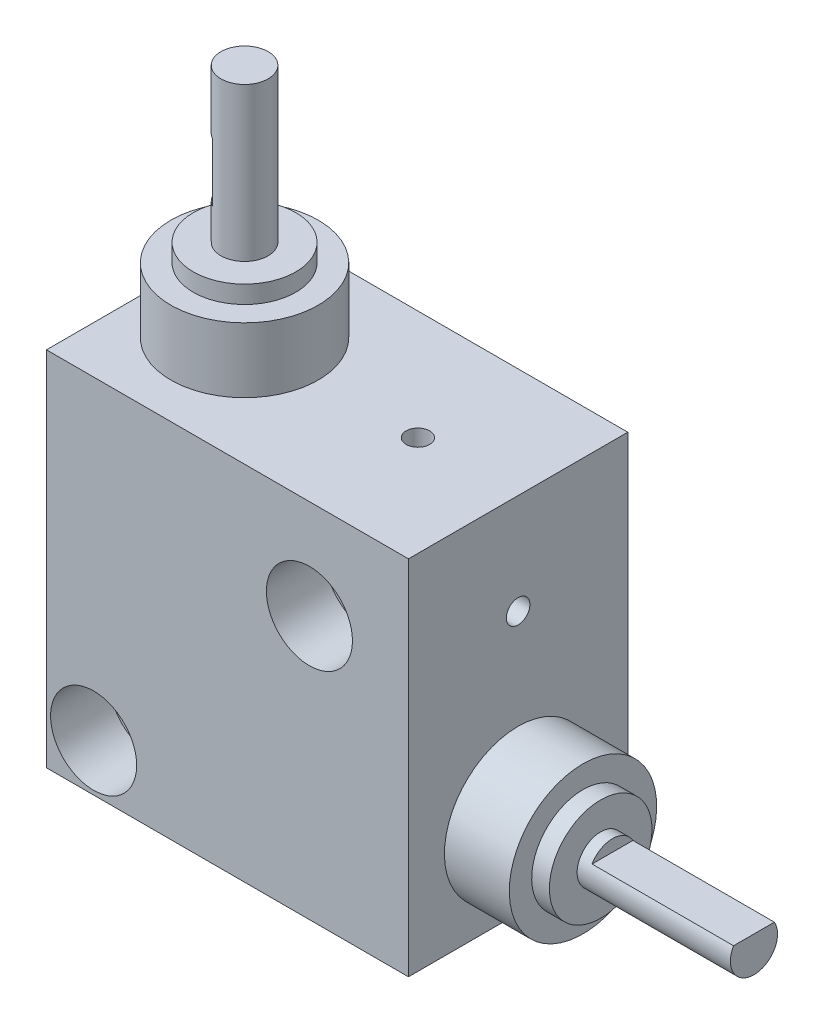
SolidWorks part; units mm, degrees
ref_plane "Plan de face" through (0, 0, 0) normal (0, 0, 1) x (1, 0, 0)
ref_plane "Plan de dessus" through (0, 0, 0) normal (0, 1, 0) x (1, 0, 0)
ref_plane "Plan de droite" through (0, 0, 0) normal (1, 0, 0) x (0, 0, -1)
sketch "Esquisse1" plane through (0, 0, 0) normal (0, 0, 1) x (1, 0, 0)
  line L1 (0, 0) -> (30.7, 0)
  line L2 (0, 0) -> (0, 30.7)
  line L3 (0, 30.7) -> (30.7, 30.7)
  line L4 (30.7, 0) -> (30.7, 30.7)
  dimension "D1" = 30.7
  dimension "D2" = 30.7
extrude "Boss.-Extru.1" add sketch "Esquisse1" along normal mid plane 18.6
sketch "Esquisse2" plane through (0, 0, 9.3) normal (0, 0, 1) x (1, 0, 0)
  line L0 (0, 0) -> (30.7, 0) construction
  line L2 (30.7, 0) -> (30.7, 30.7) construction
  line L3 (30.7, 30.7) -> (0, 30.7) construction
  line L5 (0, 30.7) -> (0, 0) construction
  circle A0 centre (4, 4) radius 2
  circle A1 centre (22.3, 22.3) radius 2
  dimension "D1" = 4
  dimension "D4" = 4
  dimension "D2" = 4
  dimension "D3" = 26.7
  dimension "D5" = 8.4
  dimension "D6" = 8.4
  dimension "D7" = 26.7
  dimension "D8" = 22.3
  dimension "D9" = 22.3
extrude "Enlèv. mat.-Extru.1" cut sketch "Esquisse2" against normal through all
sketch "Esquisse3" plane through (0, 0, 9.3) normal (0, 0, 1) x (1, 0, 0)
  circle A0 centre (4, 4) radius 3.65
  circle A1 centre (4, 4) radius 2 construction
  circle A2 centre (22.3, 22.3) radius 3.65
  circle A3 centre (22.3, 22.3) radius 2 construction
  dimension "D1" = 7.3
extrude "Enlèv. mat.-Extru.2" cut sketch "Esquisse3" against normal blind 5
sketch "Esquisse4" plane through (0, 0, -9.3) normal (0, 0, -1) x (-1, 0, 0)
  circle A0 centre (-4, 4) radius 3.65
  circle A1 centre (-22.3, 22.3) radius 3.65
  circle A2 centre (-22.3, 22.3) radius 2 construction
  dimension "D1" = 7.3
  dimension "D2" = 7.3
extrude "Enlèv. mat.-Extru.3" cut sketch "Esquisse4" against normal blind 5
sketch "Esquisse6" plane through (0, 0, 0) normal (0, 0, 1) x (1, 0, 0)
  line L0 (30.7, 13.75) -> (36.2, 13.75)
  line L1 (36.2, 13.75) -> (36.2, 11.85)
  line L2 (36.2, 11.85) -> (37.7, 11.85)
  line L3 (37.7, 11.85) -> (37.7, 9.5)
  line L4 (37.7, 9.5) -> (50.7, 9.5)
  line L5 (50.7, 9.5) -> (50.7, 7.5)
  line L6 (50.7, 7.5) -> (30.7, 7.5)
  line L7 (30.7, 0) -> (30.7, 30.7) construction
  line L8 (30.7, 7.5) -> (30.7, 13.75)
  line L9 (0, 0) -> (30.7, 0) construction
  dimension "D1" = 2
  dimension "D2" = 20
  dimension "D3" = 5.5
  dimension "D4" = 1.5
  dimension "D5" = 6.25
  dimension "D6" = 7.5
  dimension "D7" = 4.35
revolve "Révolution1" add sketch "Esquisse6" angle 360 about L6
sketch "Esquisse8" plane through (0, 0, 0) normal (0, 0, 1) x (1, 0, 0)
  line L0 (1.25, 30.7) -> (1.25, 36.2)
  line L1 (1.25, 36.2) -> (3.15, 36.2)
  line L2 (3.15, 36.2) -> (3.15, 37.7)
  line L3 (3.15, 37.7) -> (5.5, 37.7)
  line L4 (5.5, 37.7) -> (5.5, 50.7)
  line L5 (5.5, 50.7) -> (7.5, 50.7)
  line L6 (7.5, 50.7) -> (7.5, 30.7)
  line L7 (7.5, 30.7) -> (1.25, 30.7)
  line L8 (30.7, 30.7) -> (0, 30.7) construction
  line L9 (0, 30.7) -> (0, 0) construction
  dimension "D1" = 2
  dimension "D2" = 1.5
  dimension "D3" = 5.5
  dimension "D4" = 20
  dimension "D5" = 6.25
  dimension "D6" = 4.35
  dimension "D7" = 7.5
  dimension "D8" = 0
revolve "Révolution2" add sketch "Esquisse8" angle 360 about L6
ref_plane "Plan1" through (0, 45.7, 0) normal (0, 1, 0) x (1, 0, 0)
sketch "Esquisse9" plane through (0, 45.7, 0) normal (0, 1, 0) x (1, 0, 0)
  line L0 (6.5, -2) -> (5.5, -2)
  line L1 (5.5, -2) -> (5.5, 2)
  line L3 (5.5, 2) -> (6.5, 2)
  line L4 (6.5, -2) -> (6.5, 2)
  circle A0 centre (7.5, 0) radius 2 construction
  point P2 (5.5, 0)
  dimension "D1" = 1
  dimension "D2" = 4
extrude "Enlèv. mat.-Extru.4" cut sketch "Esquisse9" against normal blind 5
ref_plane "Plan2" through (50.7, 0, 0) normal (1, 0, 0) x (0, 0, -1)
sketch "Esquisse10" plane through (50.7, 0, 0) normal (1, 0, 0) x (0, 0, -1)
  line L1 (-2, 9.5) -> (2, 9.5)
  line L2 (-2, 9.5) -> (-2, 8.5)
  line L3 (-2, 8.5) -> (2, 8.5)
  line L4 (2, 9.5) -> (2, 8.5)
  circle A0 centre (0, 7.5) radius 2 construction
  point P6 (0, 9.5)
  dimension "D1" = 1
  dimension "D2" = 4
extrude "Enlèv. mat.-Extru.5" cut sketch "Esquisse10" against normal blind 12
sketch "Esquisse11" plane through (30.7, 0, 0) normal (1, 0, 0) x (0, 0, -1)
  line L0 (-9.3, 30.7) -> (9.3, 30.7) construction
  circle A0 centre (0, 22.2) radius 1
  dimension "D1" = 8.5
  dimension "D2" = 2
extrude "Enlèv. mat.-Extru.6" cut sketch "Esquisse11" against normal blind 5
sketch "Esquisse13" plane through (0, 30.7, 0) normal (0, 1, 0) x (1, 0, 0)
  line L0 (30.7, -9.3) -> (30.7, 9.3) construction
  circle A0 centre (22.2, 0) radius 1
  point P4 (30.7, 0)
  dimension "D1" = 2
  dimension "D2" = 8.5
extrude "Enlèv. mat.-Extru.7" cut sketch "Esquisse13" against normal blind 5
